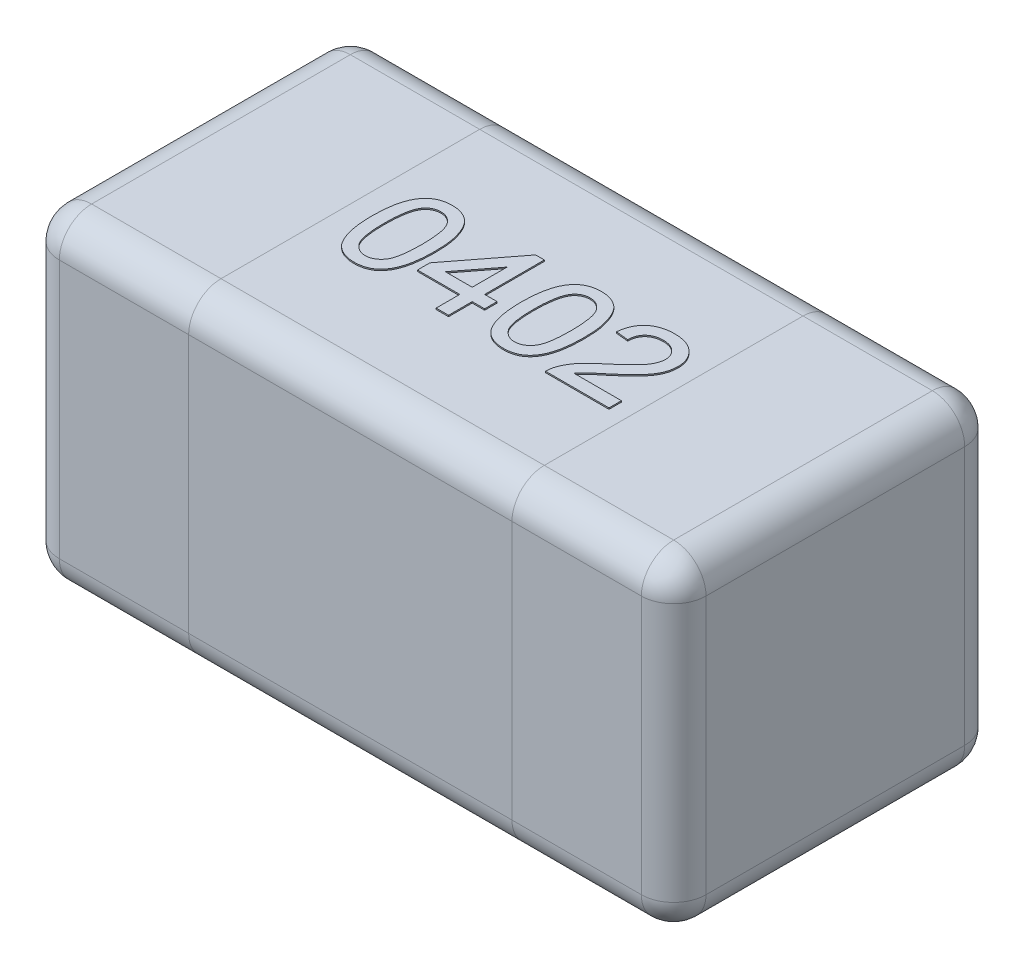
SolidWorks part; units mm, degrees
ref_plane "Front" through (0, 0, 0) normal (0, 0, 1) x (1, 0, 0)
ref_plane "Top" through (0, 0, 0) normal (0, 1, 0) x (1, 0, 0)
ref_plane "Right" through (0, 0, 0) normal (1, 0, 0) x (0, 0, -1)
sketch "Sketch1" plane through (0, 0, 0) normal (0, 1, 0) x (1, 0, 0)
  line L0 (0, -5.3126) -> (0, 5.729) construction
  line L1 (-6.1479, 0) -> (7.7291, 0) construction
  line L3 (-0.5, 0.25) -> (0.5, 0.25)
  line L4 (-0.5, 0.25) -> (-0.5, -0.25)
  line L5 (-0.5, -0.25) -> (0.5, -0.25)
  line L6 (0.5, 0.25) -> (0.5, -0.25)
  dimension "D1" = 1
  dimension "D2" = 0.5
extrude "Extrude1" add sketch "Sketch1" along normal blind 0.5
fillet "Fillet1" radius 0.05 12 edges at (0, 0.5, 0.25) (-0.5, 0.25, -0.25) (0, 0, -0.25) (-0.5, 0, 0) (-0.5, 0.25, 0.25) (0, 0, 0.25) (0.5, 0.25, 0.25) (0.5, 0.25, -0.25) (0.5, 0, 0) (0, 0.5, -0.25) (0.5, 0.5, 0) (-0.5, 0.5, 0)
sketch "Sketch2" plane through (0, 0, 0.25) normal (0, 0, 1) x (1, 0, 0)
  line L0 (-0.45, 0.5) -> (0.45, 0.5) construction
  line L1 (-0.25, 0.5) -> (0.25, 0.5)
  line L2 (-0.25, 0.5) -> (-0.25, 0)
  line L3 (-0.25, 0) -> (0.25, 0)
  line L4 (0.25, 0.5) -> (0.25, 0)
  line L5 (0.45, 0) -> (-0.45, 0) construction
  line L6 (-0.5, 0.05) -> (-0.5, 0.45) construction
  line L7 (0, -0.2963) -> (0, 3.0124) construction
  dimension "D1" = 0.25
split line "Split Line1"
sketch "Sketch3" plane through (0, 0.5, 0) normal (0, 1, 0) x (1, 0, 0)
  text T0 "0402" font "Arial" height 0.15
  dimension "D1" = 0.225
  dimension "D2" = 0.075
extrude "Extrude2" add sketch "Sketch3" along normal blind 0.002
